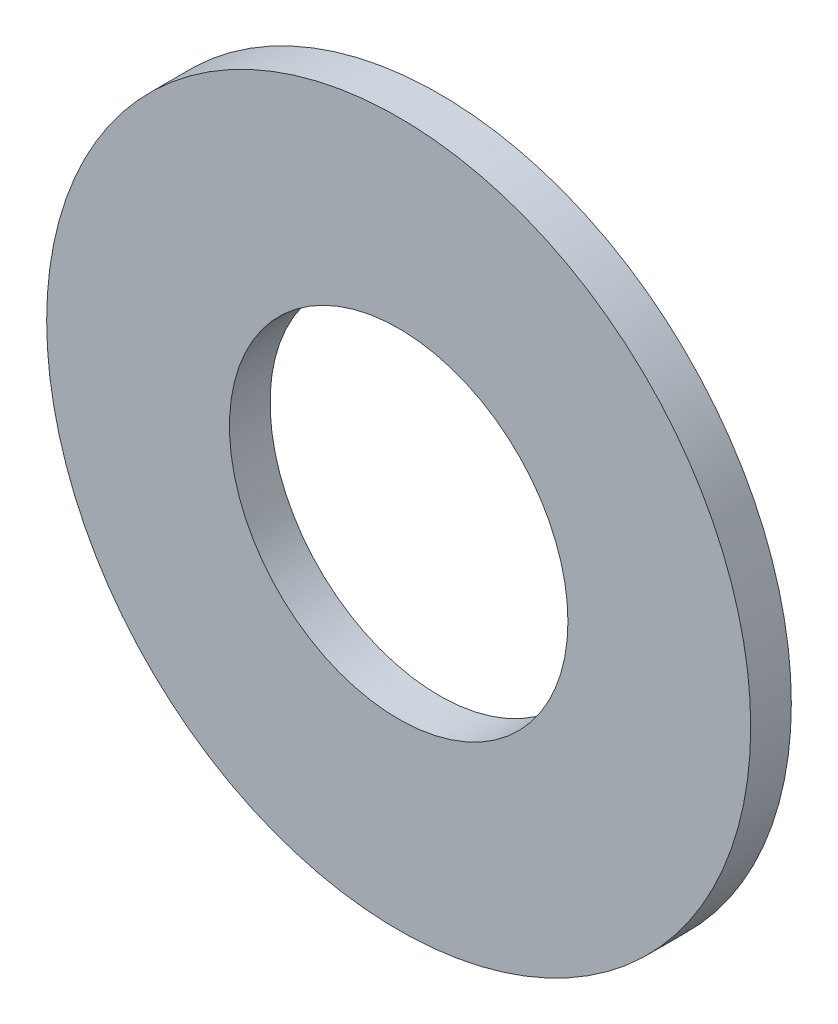
SolidWorks part; units mm, degrees
ref_plane "Front Plane" through (0, 0, 0) normal (0, 0, 1) x (1, 0, 0)
ref_plane "Top Plane" through (0, 0, 0) normal (0, 1, 0) x (1, 0, 0)
ref_plane "Right Plane" through (0, 0, 0) normal (1, 0, 0) x (0, 0, -1)
sketch "Sketch1" plane through (0, 0, 0) normal (0, 0, 1) x (1, 0, 0)
  circle A0 centre (0, 0) radius 26
  circle A1 centre (0, 0) radius 12.5
  dimension "D1" = 52
  dimension "D2" = 25
extrude "Boss-Extrude1" add sketch "Sketch1" along normal blind 3
